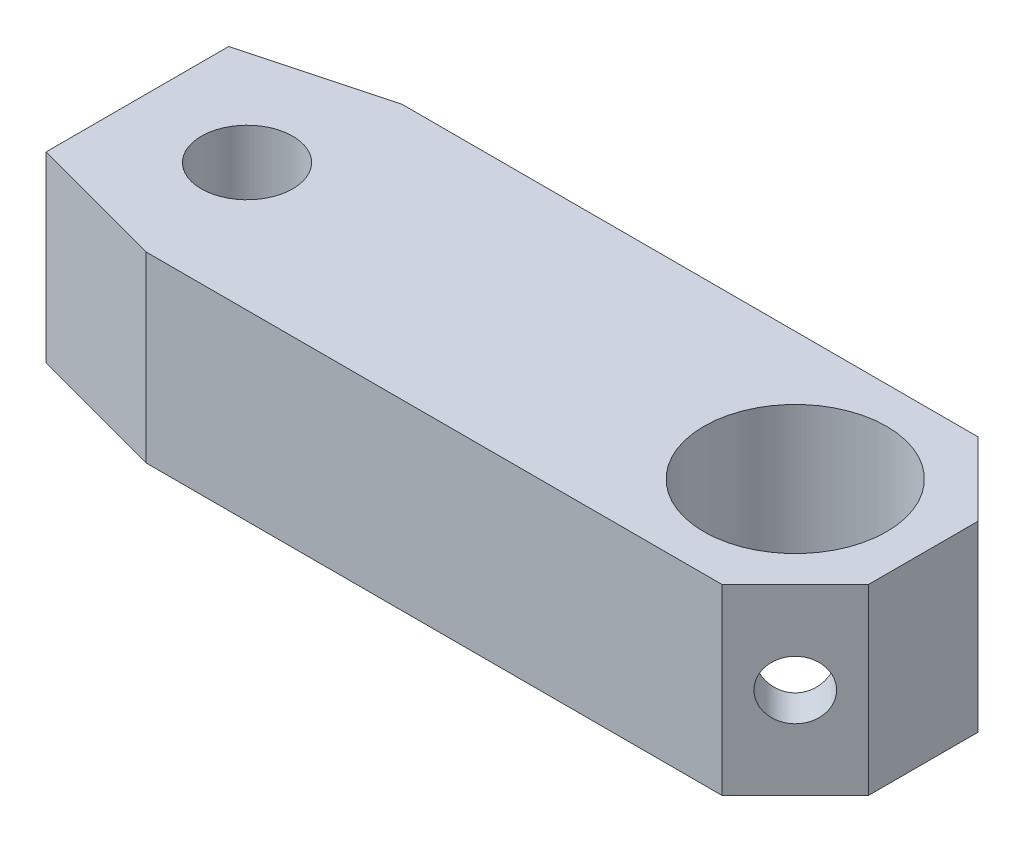
SolidWorks part; units mm, degrees
ref_plane "Front Plane" through (0, 0, 0) normal (0, 0, 1) x (1, 0, 0)
ref_plane "Top Plane" through (0, 0, 0) normal (0, 1, 0) x (1, 0, 0)
ref_plane "Right Plane" through (0, 0, 0) normal (1, 0, 0) x (0, 0, -1)
sketch "block" plane through (0, 0, 0) normal (0, 1, 0) x (1, 0, 0)
  line L0 (15, 0) -> (18.5, 3.5) construction
  line L1 (0.7321, 3.5) -> (16.5, 3.5)
  line L2 (-3, 2.5) -> (-3, -2.5)
  line L3 (0.7321, -3.5) -> (16.5, -3.5)
  line L4 (18.5, 1.5) -> (18.5, -1.5)
  line L5 (-3, 3.5) -> (18.5, -3.5) construction
  line L6 (-3, -3.5) -> (18.5, 3.5) construction
  line L7 (16.5, 3.5) -> (18.5, 1.5)
  line L8 (-3, -2.5) -> (0.7321, -3.5)
  line L9 (0.7321, 3.5) -> (-3, 2.5)
  line L10 (16.5, -3.5) -> (18.5, -1.5)
  circle A0 centre (15, 0) radius 2.5
  point P0 (0, 0)
  point P4 (7.75, 0)
  point P11 (17.5, 2.5)
  point P21 (17.5, -2.5)
  dimension "D2" = 5
  dimension "D1" = 15
  dimension "D3" = 0
  dimension "D4" = 0
  dimension "D5" = 3
  dimension "D6" = 3.5
  dimension "D7" = 3.5
  dimension "D8" = 26.966
  dimension "D9" = 2
  dimension "D10" = 45
  dimension "D11" = 1
  dimension "D12" = 75
  dimension "D13" = 1
  dimension "D14" = 75
  dimension "D15" = 2
  dimension "D16" = 45
extrude "Boss-Extrude1" add sketch "block" against normal blind 5 contours L1 L9 L2 L8 L3 L4 L7 A0
hole_wizard "M3 Tapped Hole1" positions "Sketch4" profile "Sketch5" tap size "M3" standard "ISO" end condition through all
sketch "Sketch4" plane through (0, 0, 0) normal (0, 1, 0) x (1, 0, 0)
  line L0 (0, -2.75) -> (0, 2.75) construction
  line L1 (-2.75, 0) -> (2.75, 0) construction
  point P0 (0, 0)
  dimension "D1" = 0
  dimension "D2" = 0
sketch "Sketch5" plane through (0, 0, 0) normal (1, 0, 0) x (0, 0, 1)
  line L0 (0, 0) -> (0, 5)
  line L1 (0, 5) -> (1.25, 5)
  line L2 (1.25, 5) -> (1.25, 0)
  line L5 (1.25, 0) -> (0, 0)
  line L11 (0, -6.35) -> (0, 107.95) construction
  dimension "Thru Tap Drill Dia." = 2.5
  dimension "Thru Tap Drill Depth" = 5
cosmetic thread "Hole Thread1"
hole_wizard "M2 Tapped Hole1" positions "Sketch8" profile "Sketch9" tap size "M2" standard "ISO"
sketch "Sketch8" plane through (10, 0, -10) normal (0.7071, 0, -0.7071) x (-0.7071, 0, -0.7071)
  line L0 (-10.6066, 0) -> (-10.6066, -5) construction
  line L1 (-9.1924, 0) -> (-12.0208, 0) construction
  line L2 (-9.1924, -5) -> (-12.0208, -5) construction
  line L3 (-10.6066, -5) -> (-10.6066, -2.5) construction
  line L4 (-10.6066, -2.5) -> (-12.0208, -2.5) construction
  line L5 (-12.0208, -5) -> (-12.0208, 0) construction
  point P0 (-10.6066, -2.5)
  dimension "D1" = 0
  dimension "D2" = 0
sketch "Sketch9" plane through (17.5, -2.5, -2.5) normal (0, 1, 0) x (-0.7071, 0, -0.7071)
  line L0 (0, 0) -> (0, 1.0355)
  line L1 (0, 1.0355) -> (0.8, 1.0355)
  line L2 (0.8, 1.0355) -> (0.8, 0)
  line L5 (0.8, 0) -> (0, 0)
  line L11 (0, -6.35) -> (0, 107.95) construction
  dimension "Thru Tap Drill Dia." = 1.6
  dimension "Thru Tap Drill Depth" = 1.0355
cosmetic thread "Hole Thread3"
mirror "Mirror1" about plane through (0, 0, 0) normal (0, 0, 1) of "M2 Tapped Hole1"
cosmetic thread "Hole Thread4"
equation "\"D6@block\" = \"D2@block\" / 2 + 1"
equation "\"D7@block\" = \"D2@block\" / 2 + 1"
equation "\"D1@block\"=\"D2@block\"/2+12.5mm"
